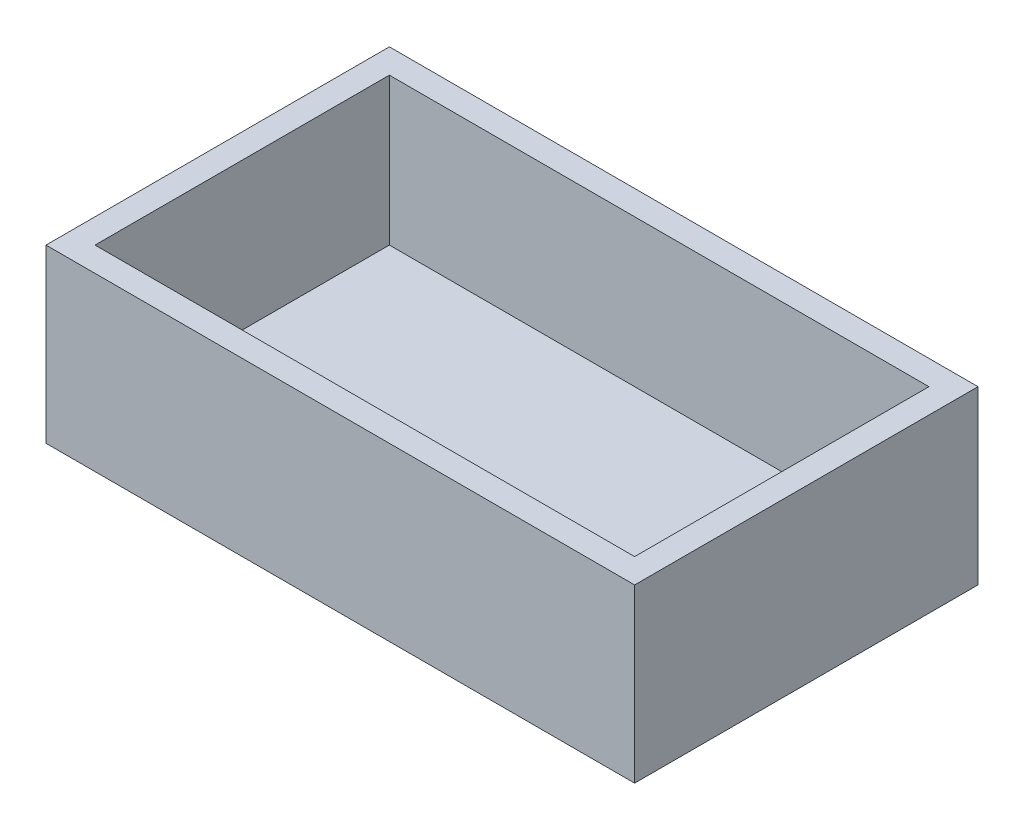
SolidWorks part; units mm, degrees
ref_plane "Front Plane" through (0, 0, 0) normal (0, 0, 1) x (1, 0, 0)
ref_plane "Top Plane" through (0, 0, 0) normal (0, 1, 0) x (1, 0, 0)
ref_plane "Right Plane" through (0, 0, 0) normal (1, 0, 0) x (0, 0, -1)
sketch "Sketch4" plane through (0, 0, 0) normal (0, 1, 0) x (1, 0, 0)
  line L1 (0, 0) -> (152.4, 0)
  line L2 (0, 0) -> (0, 88.9)
  line L3 (0, 88.9) -> (152.4, 88.9)
  line L4 (152.4, 0) -> (152.4, 88.9)
  dimension "D1" = 152.4
  dimension "D2" = 88.9
extrude "Boss-Extrude2" add sketch "Sketch4" along normal blind 44.45
sketch "Sketch6" plane through (0, 44.45, 0) normal (0, 1, 0) x (1, 0, 0)
  line L0 (0, 88.9) -> (0, 0) construction
  line L1 (6.35, 6.35) -> (146.05, 6.35)
  line L2 (6.35, 6.35) -> (6.35, 82.55)
  line L3 (6.35, 82.55) -> (146.05, 82.55)
  line L4 (146.05, 6.35) -> (146.05, 82.55)
  line L5 (0, 0) -> (152.4, 0) construction
  dimension "D1" = 6.35
  dimension "D2" = 139.7
  dimension "D3" = 6.35
  dimension "D4" = 76.2
extrude "Cut-Extrude1" cut sketch "Sketch6" against normal blind 38.1
